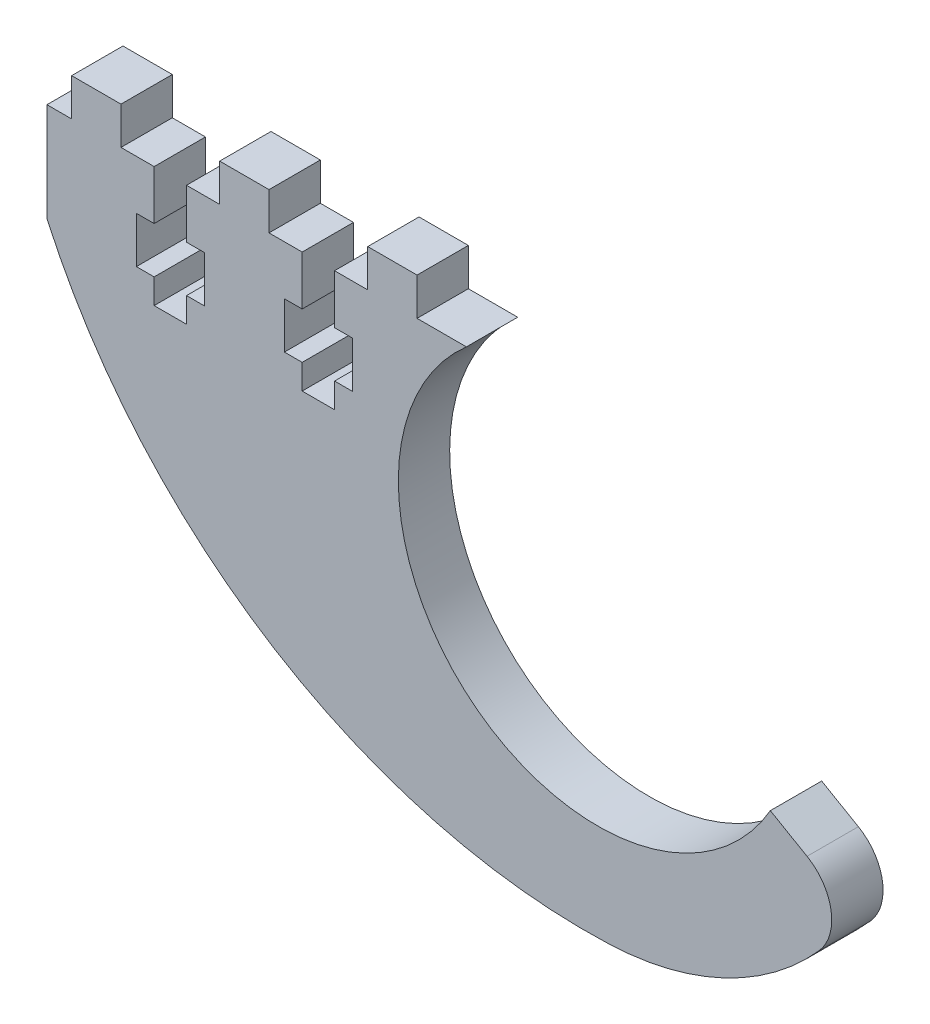
SolidWorks part; units mm, degrees
material "Acrylic (Blue)"
ref_plane "Front Plane" through (0, 0, 0) normal (0, 0, 1) x (1, 0, 0)
ref_plane "Top Plane" through (0, 0, 0) normal (0, 1, 0) x (1, 0, 0)
ref_plane "Right Plane" through (0, 0, 0) normal (1, 0, 0) x (0, 0, -1)
sketch "Sketch1" plane through (0, 0, 0) normal (0, 0, 1) x (1, 0, 0)
  line L0 (0, 0) -> (24.868, 0) construction
  line L1 (0, 0) -> (-101.6, 0) construction
  line L2 (0, 0) -> (0, -5.08) construction
  line L3 (0, -5.08) -> (-101.6, -5.08) construction
  line L4 (-101.6, 0) -> (-101.6, -5.08) construction
  line L5 (-53.975, -5.08) -> (-53.975, -17.78)
  line L6 (-6.35, -5.08) -> (0, -5.08)
  line L7 (16.8963, -24.384) -> (18.3684, -62.4555) construction
  line L8 (39.1133, -37.211) -> (49.8918, -43.434)
  line L9 (-53.975, -5.08) -> (-6.35, -5.08)
  line L10 (39.1133, -37.211) -> (16.8963, -24.384) construction
  line L11 (16.8963, -24.384) -> (89.4592, -24.384) construction
  line L12 (16.8963, -24.384) -> (-5.3208, -11.557) construction
  circle A0 centre (16.8963, -24.384) radius 25.654 construction
  arc A1 (49.8918, -43.434) -> (18.3684, -62.4555) centre (16.8963, -24.384) cw
  arc A2 (39.1133, -37.211) -> (0, -5.08) centre (16.8963, -24.384) cw
  arc A3 (-53.975, -17.78) -> (18.3684, -62.4555) centre (15.4241, 13.6875) ccw
  line B0 (-40.1828, -5.08) -> (-40.1828, -11.43) construction
  line B1 (-40.1828, -11.43) -> (-42.4688, -11.43) construction
  line B2 (-42.4688, -11.43) -> (-42.4688, -17.3736) construction
  line B3 (-42.4688, -17.3736) -> (-40.1828, -17.3736) construction
  line B4 (-40.1828, -17.3736) -> (-40.1828, -20.574) construction
  line B5 (-40.1828, -20.574) -> (-36.0172, -20.574) construction
  line B6 (-36.0172, -20.574) -> (-36.0172, -17.3736) construction
  line B7 (-36.0172, -17.3736) -> (-33.7312, -17.3736) construction
  line B8 (-33.7312, -17.3736) -> (-33.7312, -11.43) construction
  line B9 (-33.7312, -11.43) -> (-36.0172, -11.43) construction
  line B10 (-36.0172, -11.43) -> (-36.0172, -5.08) construction
  line B11 (-36.0172, -5.08) -> (-31.75, -5.08) construction
  line B12 (-31.75, -5.08) -> (-31.75, -0.254) construction
  line B13 (-31.75, -0.254) -> (-25.4, -0.254) construction
  line B14 (-25.4, -0.254) -> (-25.4, -5.08) construction
  line B15 (-40.1828, -5.08) -> (-44.45, -5.08) construction
  line B16 (-44.45, -5.08) -> (-44.45, -0.254) construction
  line B17 (-44.45, -0.254) -> (-50.8, -0.254) construction
  line B18 (-50.8, -0.254) -> (-50.8, -5.08) construction
  line B19 (-36.0172, -5.08) -> (-40.1828, -5.08) construction
  line B20 (-6.35, -0.254) -> (-6.35, -5.08) construction
  line B21 (-21.1328, -5.08) -> (-21.1328, -11.43) construction
  line B22 (-21.1328, -11.43) -> (-23.4188, -11.43) construction
  line B23 (-23.4188, -11.43) -> (-23.4188, -17.3736) construction
  line B24 (-23.4188, -17.3736) -> (-21.1328, -17.3736) construction
  line B25 (-21.1328, -17.3736) -> (-21.1328, -20.574) construction
  line B26 (-21.1328, -20.574) -> (-16.9672, -20.574) construction
  line B27 (-16.9672, -20.574) -> (-16.9672, -17.3736) construction
  line B28 (-16.9672, -17.3736) -> (-14.6812, -17.3736) construction
  line B29 (-14.6812, -17.3736) -> (-14.6812, -11.43) construction
  line B30 (-14.6812, -11.43) -> (-16.9672, -11.43) construction
  line B31 (-16.9672, -11.43) -> (-16.9672, -5.08) construction
  line B32 (-16.9672, -5.08) -> (-12.7, -5.08) construction
  line B33 (-12.7, -5.08) -> (-12.7, -0.254) construction
  line B34 (-12.7, -0.254) -> (-6.35, -0.254) construction
  line B35 (-21.1328, -5.08) -> (-25.4, -5.08) construction
  line B36 (-25.4, -5.08) -> (-25.4, -0.254) construction
  line B37 (-25.4, -0.254) -> (-31.75, -0.254) construction
  line B38 (-31.75, -0.254) -> (-31.75, -5.08) construction
  line B39 (-16.9672, -5.08) -> (-21.1328, -5.08) construction
  dimension "D2" = 51.308
  dimension "D4" = 12.7
  dimension "D5" = 38.1
  dimension "D7" = 76.2
  dimension "D1" = 5.08
  dimension "D3" = 1.27
  dimension "D6" = 3.175
  dimension "D8" = 6.35
  dimension "D9" = 24.868
  dimension "D10" = 30
  dimension "D11" = 101.6
  dimension "D12" = 16.8963
sketch_block_instance "NUT_HOLE_2X-1"
sketch_block "NUT_HOLE_2X" parameters "D1"=6.35, "D2"=4.1656, "D3"=25.4, "D4"=4.826, "D5"=8.7376, "D6"=5.9436, "D7"=6.35, "D8"=20.32, "D9"=2
extrude "Boss-Extrude1" add sketch "Sketch1" along normal blind 6.604
sketch "Sketch3" plane through (0, 0, 6.604) normal (0, 0, 1) x (1, 0, 0)
  line L1 (-44.45, -0.254) -> (-50.8, -0.254) construction
  line L2 (-44.45, -0.254) -> (-50.8, -0.254)
  line L3 (-31.75, -0.254) -> (-25.4, -0.254) construction
  line L4 (-31.75, -0.254) -> (-25.4, -0.254)
  line L5 (-12.7, -0.254) -> (-6.35, -0.254) construction
  line L6 (-12.7, -0.254) -> (-6.35, -0.254)
  line L7 (-50.8, -0.254) -> (-50.8, -5.08) construction
  line L8 (-44.45, -5.08) -> (-44.45, -0.254) construction
  line L9 (-31.75, -5.08) -> (-31.75, -0.254) construction
  line L10 (-25.4, -0.254) -> (-25.4, -5.08) construction
  line L11 (-12.7, -5.08) -> (-12.7, -0.254) construction
  line L21 (-6.35, -0.254) -> (-6.35, -5.08) construction
  line L22 (-50.8, -0.254) -> (-50.8, -5.08)
  line L23 (-44.45, -5.08) -> (-44.45, -0.254)
  line L24 (-31.75, -5.08) -> (-31.75, -0.254)
  line L25 (-25.4, -0.254) -> (-25.4, -5.08)
  line L26 (-12.7, -5.08) -> (-12.7, -0.254)
  line L27 (-6.35, -0.254) -> (-6.35, -5.08)
  line L28 (-50.8, -5.08) -> (-44.45, -5.08)
  line L29 (-31.75, -5.08) -> (-25.4, -5.08)
  line L30 (-12.7, -5.08) -> (-6.35, -5.08)
extrude "Boss-Extrude2" add sketch "Sketch3" against normal up to surface (6.604 mm away) up to face at (-3.9803, -34.8651, 0)
sketch "Sketch4" plane through (0, 0, 6.604) normal (0, 0, 1) x (1, 0, 0)
  line L22 (-40.1828, -5.08) -> (-40.1828, -11.43) construction
  line L23 (-36.0172, -11.43) -> (-36.0172, -5.08) construction
  line L24 (-33.7312, -11.43) -> (-36.0172, -11.43) construction
  line L25 (-33.7312, -17.3736) -> (-33.7312, -11.43) construction
  line L26 (-40.1828, -11.43) -> (-42.4688, -11.43) construction
  line L27 (-42.4688, -11.43) -> (-42.4688, -17.3736) construction
  line L28 (-42.4688, -17.3736) -> (-40.1828, -17.3736) construction
  line L29 (-40.1828, -17.3736) -> (-40.1828, -20.574) construction
  line L30 (-40.1828, -20.574) -> (-36.0172, -20.574) construction
  line L31 (-36.0172, -20.574) -> (-36.0172, -17.3736) construction
  line L32 (-36.0172, -17.3736) -> (-33.7312, -17.3736) construction
  line L33 (-21.1328, -11.43) -> (-23.4188, -11.43) construction
  line L34 (-21.1328, -5.08) -> (-21.1328, -11.43) construction
  line L35 (-16.9672, -11.43) -> (-16.9672, -5.08) construction
  line L36 (-14.6812, -11.43) -> (-16.9672, -11.43) construction
  line L37 (-14.6812, -17.3736) -> (-14.6812, -11.43) construction
  line L38 (-23.4188, -11.43) -> (-23.4188, -17.3736) construction
  line L39 (-23.4188, -17.3736) -> (-21.1328, -17.3736) construction
  line L40 (-21.1328, -17.3736) -> (-21.1328, -20.574) construction
  line L41 (-16.9672, -17.3736) -> (-14.6812, -17.3736) construction
  line L42 (-16.9672, -20.574) -> (-16.9672, -17.3736) construction
  line L43 (-21.1328, -20.574) -> (-16.9672, -20.574) construction
  line L44 (-40.1828, -5.08) -> (-40.1828, -11.43)
  line L45 (-36.0172, -11.43) -> (-36.0172, -5.08)
  line L47 (-33.7312, -11.43) -> (-36.0172, -11.43)
  line L48 (-33.7312, -17.3736) -> (-33.7312, -11.43)
  line L49 (-40.1828, -11.43) -> (-42.4688, -11.43)
  line L50 (-42.4688, -11.43) -> (-42.4688, -17.3736)
  line L51 (-42.4688, -17.3736) -> (-40.1828, -17.3736)
  line L52 (-40.1828, -17.3736) -> (-40.1828, -20.574)
  line L53 (-40.1828, -20.574) -> (-36.0172, -20.574)
  line L54 (-36.0172, -20.574) -> (-36.0172, -17.3736)
  line L55 (-36.0172, -17.3736) -> (-33.7312, -17.3736)
  line L56 (-21.1328, -11.43) -> (-23.4188, -11.43)
  line L57 (-21.1328, -5.08) -> (-21.1328, -11.43)
  line L58 (-16.9672, -11.43) -> (-16.9672, -5.08)
  line L59 (-14.6812, -11.43) -> (-16.9672, -11.43)
  line L60 (-14.6812, -17.3736) -> (-14.6812, -11.43)
  line L61 (-23.4188, -11.43) -> (-23.4188, -17.3736)
  line L62 (-23.4188, -17.3736) -> (-21.1328, -17.3736)
  line L63 (-21.1328, -17.3736) -> (-21.1328, -20.574)
  line L64 (-16.9672, -17.3736) -> (-14.6812, -17.3736)
  line L65 (-16.9672, -20.574) -> (-16.9672, -17.3736)
  line L66 (-21.1328, -20.574) -> (-16.9672, -20.574)
  line L67 (-36.0172, -5.08) -> (-40.1828, -5.08)
  line L68 (-16.9672, -5.08) -> (-21.1328, -5.08)
extrude "Cut-Extrude1" cut sketch "Sketch4" against normal up to next
fillet "Fillet1" radius 6.35 1 edges at (49.8918, -43.434, 3.302)
other "Move Face1" [suppressed] parameters "D1"=0.0508
